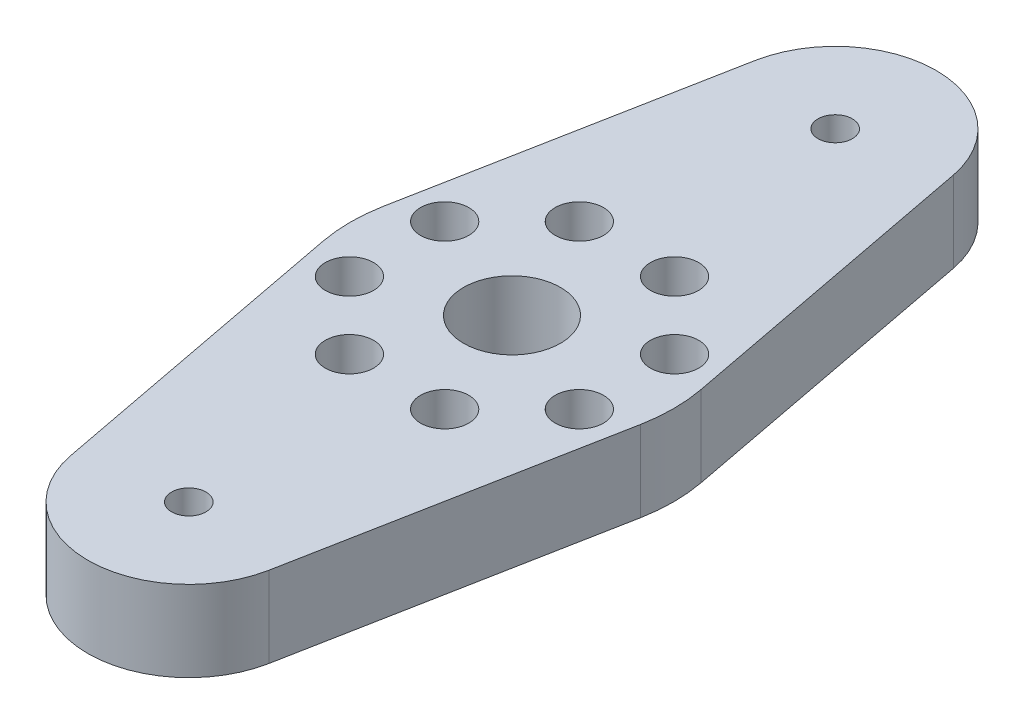
SolidWorks part; units mm, degrees
material "5052-H32"
ref_plane "Front Plane" through (0, 0, 0) normal (0, 0, 1) x (1, 0, 0)
ref_plane "Top Plane" through (0, 0, 0) normal (0, 1, 0) x (1, 0, 0)
ref_plane "Right Plane" through (0, 0, 0) normal (1, 0, 0) x (0, 0, -1)
sketch "Sketch1" plane through (0, 0, 0) normal (0, 1, 0) x (1, 0, 0)
  line L0 (0, -25.4) -> (0, 25.4) construction
  line L3 (-12.4748, 2.3812) -> (-7.7967, 26.8883)
  line L4 (7.7967, 26.8883) -> (12.4748, 2.3813)
  line L5 (12.4748, -2.3812) -> (7.7967, -26.8883)
  line L6 (-12.4748, -2.3812) -> (-7.7967, -26.8883)
  arc A0 (-7.7967, -26.8883) -> (7.7967, -26.8883) centre (0, -25.4) ccw
  arc A1 (7.7967, 26.8883) -> (-7.7967, 26.8883) centre (0, 25.4) ccw
  arc A2 (-12.4748, 2.3812) -> (-12.4748, -2.3812) centre (0, 0) ccw
  arc A4 (12.4748, -2.3812) -> (12.4748, 2.3813) centre (0, 0) ccw
  circle A5 centre (0, 0) radius 3.81
  point P2 (0, 0)
  dimension "D3" = 25.4
  dimension "D1" = 7.9375
  dimension "D4" = 7.62
  dimension "D2" = 50.8
extrude "Boss-Extrude1" add sketch "Sketch1" along normal blind 6.35
hole_wizard "#6-32 Tapped Hole1" positions "Sketch2" profile "Sketch3" tap size "#6-32" standard "ANSI Inch" end condition through all
sketch "Sketch2" plane through (0, 6.35, 0) normal (0, 1, 0) x (1, 0, 0)
  point P0 (0, -25.4)
  point P3 (0, 25.4)
sketch "Sketch3" plane through (0, 6.35, 25.4) normal (1, 0, 0) x (0, 0, 1)
  line L0 (0, 0) -> (0, 6.35)
  line L1 (0, 6.35) -> (1.3525, 6.35)
  line L2 (1.3525, 6.35) -> (1.3525, 0)
  line L5 (1.3525, 0) -> (0, 0)
  line L11 (0, -6.35) -> (0, 107.95) construction
  dimension "Thread Major Dia." = 2.7051
  dimension "Thru Tap Drill Depth" = 6.35
sketch "Sketch4" plane through (0, 6.35, 0) normal (0, 1, 0) x (1, 0, 0)
  line L1 (3.7423, -9.0346) -> (-3.7423, -9.0346)
  line L2 (3.7423, -9.0346) -> (3.7423, 9.0346)
  line L3 (3.7423, 9.0346) -> (-3.7423, 9.0346)
  line L4 (-3.7423, -9.0346) -> (-3.7423, 9.0346)
  line L5 (3.7423, -9.0346) -> (-3.7423, 9.0346) construction
  line L6 (3.7423, 9.0346) -> (-3.7423, -9.0346) construction
  point P0 (0, 0)
  dimension "D1" = 19.558
  dimension "D2" = 45
hole_wizard "#6 Clearance Hole1" positions "Sketch5" profile "Sketch6" hole size "#6" standard "ANSI Inch"
sketch "Sketch5" plane through (0, 6.35, 0) normal (0, 1, 0) x (1, 0, 0)
  point P0 (-3.7423, 9.0346)
  point P3 (3.7423, 9.0346)
  point P6 (3.7423, -9.0346)
  point P9 (-3.7423, -9.0346)
sketch "Sketch6" plane through (-3.7423, 6.35, -9.0346) normal (1, 0, 0) x (0, 0, 1)
  line L0 (0, 0) -> (0, 10.5388)
  line L1 (0, 10.5388) -> (1.8986, 9.398)
  line L2 (1.8986, 9.398) -> (1.8986, 0)
  line L5 (1.8986, 0) -> (0, 0)
  line L10 (0, 10.5388) -> (-1.8987, 9.398) construction
  line L11 (0, -6.35) -> (0, 107.95) construction
  dimension "Hole Dia." = 3.7973
  dimension "Hole Depth" = 9.398
  dimension "Drill Angle" = 118
pattern_circular "CirPattern1" count 2 over 90 about axis through (0, 0, 0) along (0, 1, 0) of "#6 Clearance Hole1"
